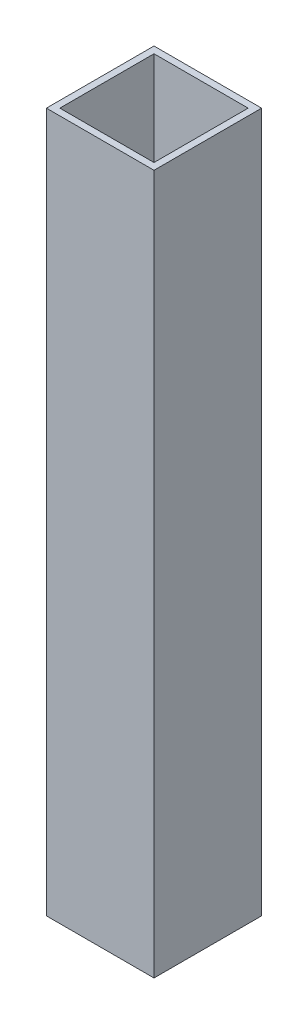
SolidWorks part; units mm, degrees
ref_plane "Front" through (0, 0, 0) normal (0, 0, 1) x (1, 0, 0)
ref_plane "Top" through (0, 0, 0) normal (0, 1, 0) x (1, 0, 0)
ref_plane "Right" through (0, 0, 0) normal (1, 0, 0) x (0, 0, -1)
sketch "Sketch1" plane through (0, 0, 0) normal (0, 1, 0) x (1, 0, 0)
  line L1 (-12.7, -12.7) -> (12.7, -12.7)
  line L2 (-12.7, -12.7) -> (-12.7, 12.7)
  line L3 (-12.7, 12.7) -> (12.7, 12.7)
  line L4 (12.7, -12.7) -> (12.7, 12.7)
  line L5 (-12.7, -12.7) -> (12.7, 12.7) construction
  line L6 (-12.7, 12.7) -> (12.7, -12.7) construction
  point P0 (0, 0)
  dimension "D1" = 25.4
  dimension "D2" = 25.4
extrude "Extrude-Thin1" add sketch "Sketch1" along normal blind 165.1 thin thin type one direction reverse wall 1.5875
